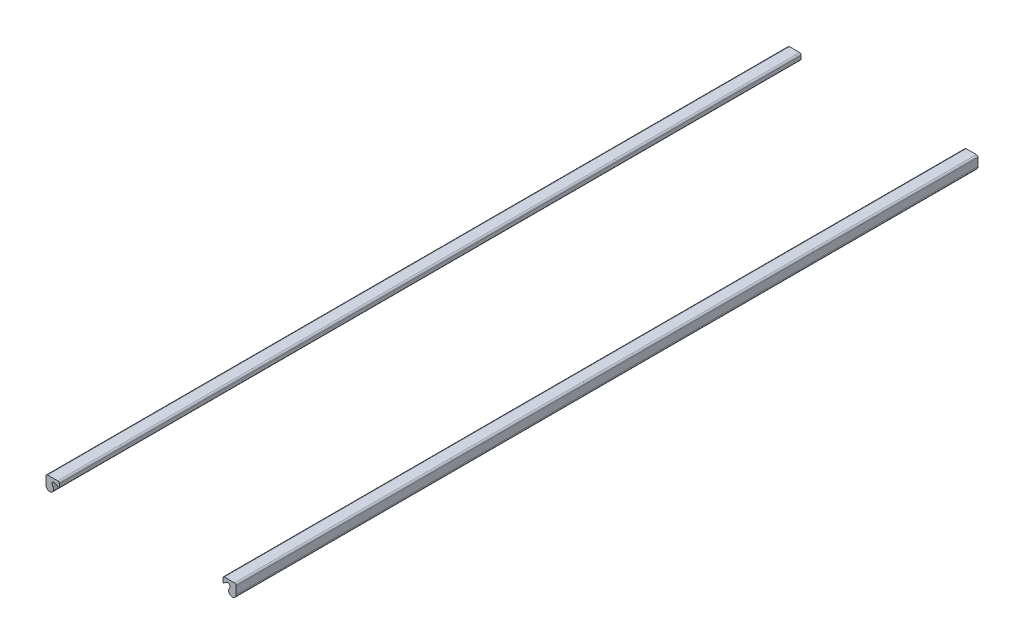
SolidWorks part; units mm, degrees
material "PUR"
ref_plane "Front Plane" through (0, 0, 0) normal (0, 0, 1) x (1, 0, 0)
ref_plane "Top Plane" through (0, 0, 0) normal (0, 1, 0) x (1, 0, 0)
ref_plane "Right Plane" through (0, 0, 0) normal (1, 0, 0) x (0, 0, -1)
sketch "Tiny Red Profile" plane through (0, 0, 0) normal (0, 0, 1) x (1, 0, 0)
  line L47 (0, 0) -> (0, 20) construction
  line L64 (6.2144, 4.9164) -> (6.4973, 4.6335) construction
  line L67 (-7.1, 4.5828) -> (-7.1, 5.18)
  line L68 (-6.98, 5.3) -> (-6.22, 5.3)
  line L69 (-6.1, 5.18) -> (-6.1, 4.9207)
  line L80 (7.1, 4.5828) -> (7.1, 5.18)
  line L81 (6.98, 5.3) -> (6.22, 5.3)
  line L82 (6.1, 5.18) -> (6.1, 4.9207)
  line L83 (6.1084, 4.5274) -> (6.6033, 5.0224) construction
  arc A31 (6.98, 5.3) -> (7.1, 5.18) centre (6.98, 5.18) cw
  arc A32 (6.1, 5.18) -> (6.22, 5.3) centre (6.22, 5.18) cw
  arc A33 (6.5781, 4.734) -> (7.1, 4.5828) centre (6.8172, 4.5828) ccw
  arc A34 (6.1, 4.9207) -> (6.1876, 4.8877) centre (6.15, 4.9207) ccw
  arc A35 (-6.1, 4.9207) -> (-6.1876, 4.8877) centre (-6.15, 4.9207) cw
  arc A36 (-6.5781, 4.734) -> (-7.1, 4.5828) centre (-6.8172, 4.5828) cw
  arc A37 (-6.98, 5.3) -> (-7.1, 5.18) centre (-6.98, 5.18) ccw
  arc A38 (-6.1, 5.18) -> (-6.22, 5.3) centre (-6.22, 5.18) ccw
  ellipse E0 centre (6.3558, 4.7749) end of major axis (6.1084, 4.5274) minor radius 0.2 (6.5781, 4.734) -> (6.1876, 4.8877) ccw
  ellipse E1 centre (-6.3558, 4.7749) end of major axis (-6.1084, 4.5274) minor radius 0.2 (-6.5781, 4.734) -> (-6.1876, 4.8877) cw
  point P89 (7.1, 5.3)
  dimension "D10" = 0.3793
  dimension "D11" = 0.7
  dimension "D12" = 0.4
  dimension "D5" = 1
  dimension "D1" = 0.2828
  dimension "D2" = 0.7172
  dimension "D3" = 135
  dimension "D4" = 0.12
  dimension "D7" = 0.1
  dimension "D8" = 5.3
  dimension "D9" = 7.1
extrude "Tiny Red" add sketch "Tiny Red Profile" against normal mid plane 55.4
